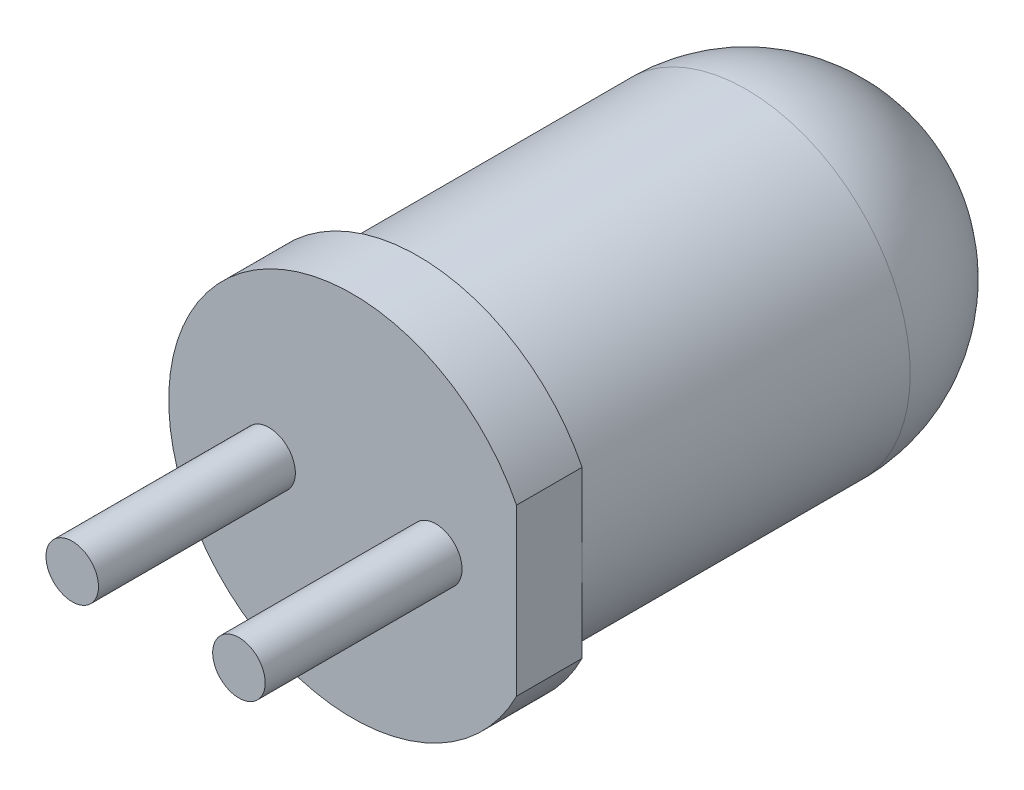
SolidWorks part; units mm, degrees
ref_plane "Face" through (0, 0, 0) normal (0, 0, 1) x (1, 0, 0)
ref_plane "Dessus" through (0, 0, 0) normal (0, 1, 0) x (1, 0, 0)
ref_plane "Droite" through (0, 0, 0) normal (1, 0, 0) x (0, 0, -1)
sketch "Esquisse1" plane through (0, 0, 0) normal (0, 0, 1) x (1, 0, 0)
  circle A0 centre (0, 0) radius 2.5
extrude "Base-Extrusion" add sketch "Esquisse1" along normal blind 8.5
sketch "Esquisse2" plane through (0, 0, 8.5) normal (0, 0, 1) x (1, 0, 0)
  line L0 (2.5, -2.4917) -> (2.5, 2.5621) construction
  line L1 (2.5, 1.261) -> (2.5, -1.261)
  arc A0 (2.5, 1.261) -> (2.5, -1.261) centre (0, 0) ccw
extrude "Boss.-Extru.1" add sketch "Esquisse2" against normal blind 1
fillet "Congé1" radius 2.5 1 edges at (2.5, 0, 0)
sketch "Esquisse3" plane through (0, 0, 8.5) normal (0, 0, 1) x (1, 0, 0)
  line L0 (2.8791, 0) -> (-3.5821, 0) construction
  line L1 (0, -2.9335) -> (0, 2.9813) construction
  line L2 (1.27, -0.8777) -> (1.27, 1.5607) construction
  circle A0 centre (1.27, 0) radius 0.4
  circle A1 centre (-1.27, 0) radius 0.4
  dimension "D1" = 1.27
extrude "Extrusion1" add sketch "Esquisse3" along normal blind 3
